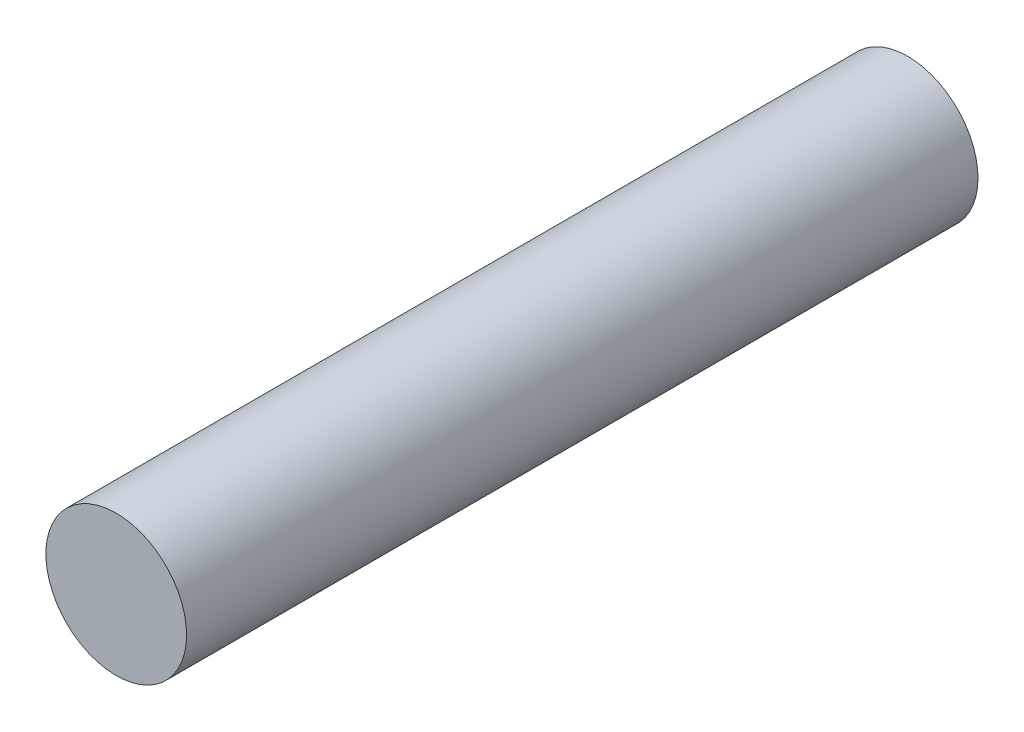
SolidWorks part; units mm, degrees
ref_plane "前视基准面" through (0, 0, 0) normal (0, 0, 1) x (1, 0, 0)
ref_plane "上视基准面" through (0, 0, 0) normal (0, 1, 0) x (1, 0, 0)
ref_plane "右视基准面" through (0, 0, 0) normal (1, 0, 0) x (0, 0, -1)
sketch "草图1" plane through (0, 0, 0) normal (0, 0, 1) x (1, 0, 0)
  circle A0 centre (0, 0) radius 4
extrude "凸台-拉伸1" add sketch "草图1" along normal blind 45
